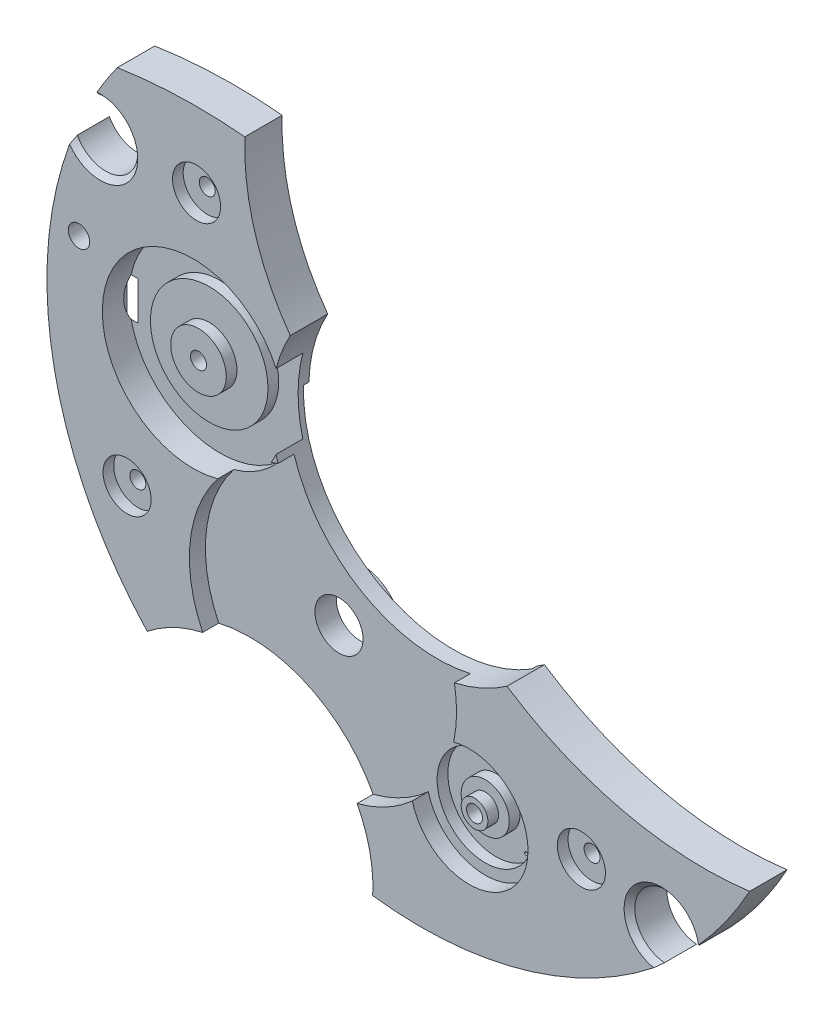
SolidWorks part; units mm, degrees
ref_plane "Alzado" through (0, 0, 0) normal (0, 0, 1) x (1, 0, 0)
ref_plane "Planta" through (0, 0, 0) normal (0, 1, 0) x (1, 0, 0)
ref_plane "Vista lateral" through (0, 0, 0) normal (1, 0, 0) x (0, 0, -1)
sketch "Croquis2" plane through (0, 0, 0) normal (0, 0, 1) x (1, 0, 0)
  line L0 (-4.5875, -7.9458) -> (0, 0) construction
  line L1 (0, 0) -> (0, -5.729) construction
  arc A0 (-16.3267, 6.3) -> (-12.8094, -11.9235) centre (0, 0) ccw
  arc A1 (-16.3267, 6.3) -> (-15.3157, 8.4664) centre (-15, 7) ccw
  arc A2 (-14.2072, 10.2179) -> (-15.3157, 8.4664) centre (0, 0) ccw
  arc A3 (-8.243, 10.3958) -> (-14.2072, 10.2179) centre (-10.5, -14) ccw
  arc A4 (-8.243, 10.3958) -> (-6.1152, 3.4064) centre (3, 10) ccw
  arc A5 (-6.1152, 3.4064) -> (4.0223, -5.729) centre (0, 0) ccw
  arc A6 (4.0223, -5.729) -> (15.3712, -8.3651) centre (13.25, 8.25) ccw
  circle A7 centre (-4.5875, -7.9458) radius 1.125
  circle A9 centre (-16, 2.5) radius 0.5
  arc A10 (-2.2596, -17.3535) -> (-12.8094, -11.9235) centre (-8.75, -17) ccw
  arc A11 (-2.2596, -17.3535) -> (11.1404, -13.496) centre (0, 0) ccw
  arc A12 (12.7499, -11.987) -> (15.3712, -8.3651) centre (0, 0) ccw
  arc A13 (12.7499, -11.987) -> (11.1404, -13.496) centre (11.25, -12) ccw
  dimension "D1" = 7
  dimension "D2" = 11.25
  dimension "D3" = 16.75
  dimension "D8" = 17.5
  dimension "D9" = 2.25
  dimension "D10" = 1.5
  dimension "D11" = 1.5
  dimension "D12" = 6.5
  dimension "D15" = 24.5
  dimension "D24" = 1
  dimension "D4" = 13.25
  dimension "D5" = 8.25
  dimension "D6" = 3
  dimension "D7" = 10
  dimension "D13" = 8.75
  dimension "D14" = 17
  dimension "D16" = 14
  dimension "D17" = 10.5
  dimension "D18" = 15
  dimension "D19" = 7
  dimension "D20" = 9.175
  dimension "D21" = 30
  dimension "D22" = 12
  dimension "D23" = 11.25
  dimension "D25" = 16
  dimension "D26" = 2.5
extrude "Saliente-Extruir1" add sketch "Croquis2" along normal blind 1.75
sketch "Croquis3" plane through (0, 0, 1.75) normal (0, 0, 1) x (1, 0, 0)
  line L0 (-4.5875, -7.9458) -> (2.2541, -11.8958) construction
  line L1 (-4.5875, -7.9458) -> (0.5327, -7.9458) construction
  arc A0 (1.5262, -9.2439) -> (-0.4065, -12.5914) centre (-4.5875, -7.9458) ccw
  arc A1 (-0.4065, -12.5914) -> (1.5262, -9.2439) centre (2.2541, -11.8958) ccw
  point P5 (0, 0)
  dimension "D1" = 12.5
  dimension "D2" = 5.5
  dimension "D3" = 30
  dimension "D4" = 7.9
extrude "Cortar-Extruir1" cut sketch "Croquis3" against normal blind 0.75
sketch "Croquis4" plane through (0, 0, 0) normal (0, 0, -1) x (-1, 0, 0)
  circle A0 centre (4.5875, -7.9458) radius 8.5
  dimension "D1" = 17
extrude "Cortar-Extruir2" cut sketch "Croquis4" against normal blind 0.25
sketch "Croquis5" plane through (0, 0, 1) normal (0, 0, 1) x (1, 0, 0)
  circle A0 centre (2.2541, -11.8958) radius 2.25
  circle A1 centre (2.2541, -11.8958) radius 1.125
  arc A2 (-0.4065, -12.5914) -> (1.5262, -9.2439) centre (2.2541, -11.8958) ccw construction
  dimension "D1" = 4.5
  dimension "D2" = 2.25
extrude "Cortar-Extruir3" cut sketch "Croquis5" against normal blind 0.5
sketch "Croquis6" plane through (0, 0, 1) normal (0, 0, 1) x (1, 0, 0)
  circle A0 centre (2.2541, -11.8958) radius 0.625
  circle A1 centre (2.2541, -11.8958) radius 1.125 construction
  dimension "D1" = 1.25
extrude "Saliente-Extruir2" add sketch "Croquis6" along normal blind 0.5
sketch "Croquis7" plane through (0, 0, 1.75) normal (0, 0, 1) x (1, 0, 0)
  line L0 (-10.6591, 0) -> (-4.5875, -7.9458) construction
  circle A0 centre (-10.6591, 0) radius 4.25
  dimension "D1" = 8.5
  dimension "D2" = 10
extrude "Cortar-Extruir4" cut sketch "Croquis7" against normal blind 1.25
sketch "Croquis8" plane through (0, 0, 0.5) normal (0, 0, 1) x (1, 0, 0)
  circle A0 centre (-10.6591, 0) radius 2.75
  circle A1 centre (-10.6591, 0) radius 4.25 construction
  dimension "D1" = 5.5
extrude "Saliente-Extruir3" add sketch "Croquis8" along normal blind 0.5
sketch "Croquis9" plane through (0, 0, 1) normal (0, 0, 1) x (1, 0, 0)
  circle A0 centre (-10.6591, 0) radius 1.3
  circle A1 centre (-10.6591, 0) radius 2.75 construction
  dimension "D1" = 2.6
extrude "Saliente-Extruir4" add sketch "Croquis9" along normal blind 0.5
sketch "Croquis10" plane through (0, 0, 0.5) normal (0, 0, 1) x (1, 0, 0)
  line L0 (3.6683, -13.31) -> (2.2541, -11.8958) construction
  line L1 (2.2541, -11.8958) -> (4.249, -11.8958) construction
  circle A0 centre (3.6683, -13.31) radius 0.075
  circle A1 centre (2.2541, -11.8958) radius 0.625 construction
  dimension "D1" = 0.15
  dimension "D2" = 2
  dimension "D3" = 45
extrude "Cortar-Extruir5" cut sketch "Croquis10" against normal through all
sketch "Croquis11" plane through (0, 0, 1.75) normal (0, 0, 1) x (1, 0, 0)
  circle A0 centre (-13.75, -6.5) radius 1.125
  circle A1 centre (-10.5, 7) radius 1.125
  circle A2 centre (7.5, -11) radius 1.125
  dimension "D1" = 2.25
  dimension "D2" = 2.25
  dimension "D3" = 2.25
  dimension "D4" = 13.75
  dimension "D5" = 6.5
  dimension "D6" = 7
  dimension "D7" = 10.5
  dimension "D8" = 11
  dimension "D9" = 7.5
extrude "Cortar-Extruir6" cut sketch "Croquis11" against normal blind 0.5
hole_wizard "Taladro roscado M1x0.251" positions "Croquis13" profile "Croquis12" tap size "M1x0.25" standard "KS" end condition through all
sketch "Croquis13" plane through (0, 0, 1.5) normal (0, 0, 1) x (1, 0, 0)
  circle A0 centre (2.2541, -11.8958) radius 0.625 construction
  point P0 (2.2541, -11.8958)
sketch "Croquis12" plane through (2.2541, -11.8958, 1.5) normal (1, 0, 0) x (0, -1, 0)
  line L0 (0, 0) -> (0, 1.5)
  line L1 (0, 1.5) -> (0.375, 1.5)
  line L2 (0.375, 1.5) -> (0.375, 0)
  line L5 (0.375, 0) -> (0, 0)
  line L11 (0, -6.35) -> (0, 107.95) construction
  dimension "Diámetro de perforador para roscar hasta el siguiente" = 0.75
  dimension "Profundidad de perforador para roscar hasta el siguiente" = 1.5
cosmetic thread "Rosca de taladro4" parameters "D2"=1
hole_wizard "Taladro roscado M1x0.253" positions "Croquis15" profile "Croquis14" tap size "M1x0.25" standard "KS" end condition through all
sketch "Croquis15" plane through (0, 0, 1.5) normal (0, 0, 1) x (1, 0, 0)
  circle A0 centre (-10.6591, 0) radius 1.3 construction
  point P0 (-10.6591, 0)
sketch "Croquis14" plane through (-10.6591, 0, 1.5) normal (1, 0, 0) x (0, -1, 0)
  line L0 (0, 0) -> (0, 1.5)
  line L1 (0, 1.5) -> (0.375, 1.5)
  line L2 (0.375, 1.5) -> (0.375, 0)
  line L5 (0.375, 0) -> (0, 0)
  line L11 (0, -6.35) -> (0, 107.95) construction
  dimension "Diámetro de perforador para roscar hasta el siguiente" = 0.75
  dimension "Profundidad de perforador para roscar hasta el siguiente" = 1.5
cosmetic thread "Rosca de taladro5" parameters "D2"=1
chamfer "Chaflán1" distance 0.25 angle 45 2 edges at (10.2241, -10.9057, 1.75) (-13.6407, 6.3657, 1.75)
sketch "Croquis16" plane through (0, 0, 0.25) normal (0, 0, -1) x (-1, 0, 0)
  circle A0 centre (4.5875, -7.9458) radius 1.125 construction
  circle A1 centre (4.5875, -7.9458) radius 1.125
  circle A2 centre (4.5875, -7.9458) radius 2
  dimension "D1" = 4
extrude "Saliente-Extruir5" add sketch "Croquis16" along normal blind 0.25
ref_plane "Plano1" through (-14.5, 0, 0) normal (1, 0, 0) x (0, 0, -1)
sketch "Croquis19" plane through (-14.5, 0, 0) normal (1, 0, 0) x (0, 0, -1)
  line L0 (-1.75, 3.4064) -> (-1.75, 1.7381) construction
  circle A0 centre (1, 0) radius 1.75
  dimension "D1" = 3.5
  dimension "D2" = 2.75
extrude "Cortar-Extruir7" cut sketch "Croquis19" against normal blind 1
sketch "Croquis20" plane through (-14.5, 0, 0) normal (-1, 0, 0) x (0, 0, 1)
  circle A0 centre (-1, 0) radius 1.25
  arc A1 (0.5, 0.9014) -> (0, 1.4361) centre (-1, 0) ccw construction
  dimension "D1" = 2.5
extrude "Cortar-Extruir8" cut sketch "Croquis20" against normal blind 3
hole_wizard "Taladro roscado M1x0.252" positions "Croquis22" profile "Croquis23" tap size "M1x0.25" standard "KS" end condition through all
sketch "Croquis22" plane through (0, 0, 1.25) normal (0, 0, 1) x (1, 0, 0)
  circle A1 centre (-13.75, -6.5) radius 1.125 construction
  circle A2 centre (-10.5, 7) radius 1.125 construction
  circle A3 centre (7.5, -11) radius 1.125 construction
  point P0 (-13.75, -6.5)
  point P1 (-10.5, 7)
  point P4 (7.5, -11)
sketch "Croquis23" plane through (-13.75, -6.5, 1.25) normal (1, 0, 0) x (0, -1, 0)
  line L0 (0, 0) -> (0, 1.25)
  line L1 (0, 1.25) -> (0.375, 1.25)
  line L2 (0.375, 1.25) -> (0.375, 0)
  line L5 (0.375, 0) -> (0, 0)
  line L11 (0, -6.35) -> (0, 107.95) construction
  dimension "Diámetro de perforador para roscar hasta el siguiente" = 0.75
  dimension "Profundidad de perforador para roscar hasta el siguiente" = 1.25
cosmetic thread "Rosca de taladro1" parameters "D2"=1
cosmetic thread "Rosca de taladro2" parameters "D2"=1
cosmetic thread "Rosca de taladro3" parameters "D2"=1
